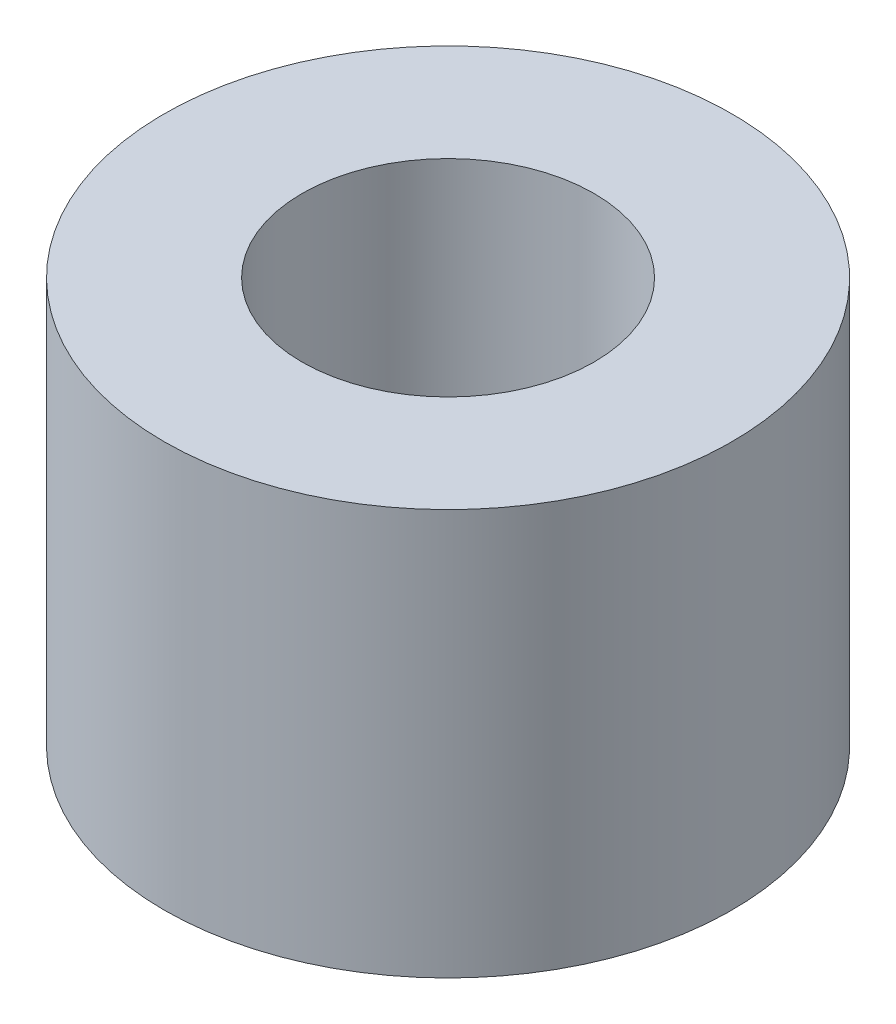
SolidWorks part; units mm, degrees
material "Nylon 101"
ref_plane "Front Plane" through (0, 0, 0) normal (0, 0, 1) x (1, 0, 0)
ref_plane "Top Plane" through (0, 0, 0) normal (0, 1, 0) x (1, 0, 0)
ref_plane "Right Plane" through (0, 0, 0) normal (1, 0, 0) x (0, 0, -1)
sketch "Sketch1" plane through (0, 0, 0) normal (0, 1, 0) x (1, 0, 0)
  circle A0 centre (0, 0) radius 3.5
  circle A1 centre (0, 0) radius 1.8
  dimension "D1" = 3.6
  dimension "D2" = 7
extrude "Boss-Extrude1" add sketch "Sketch1" along normal mid plane 5
